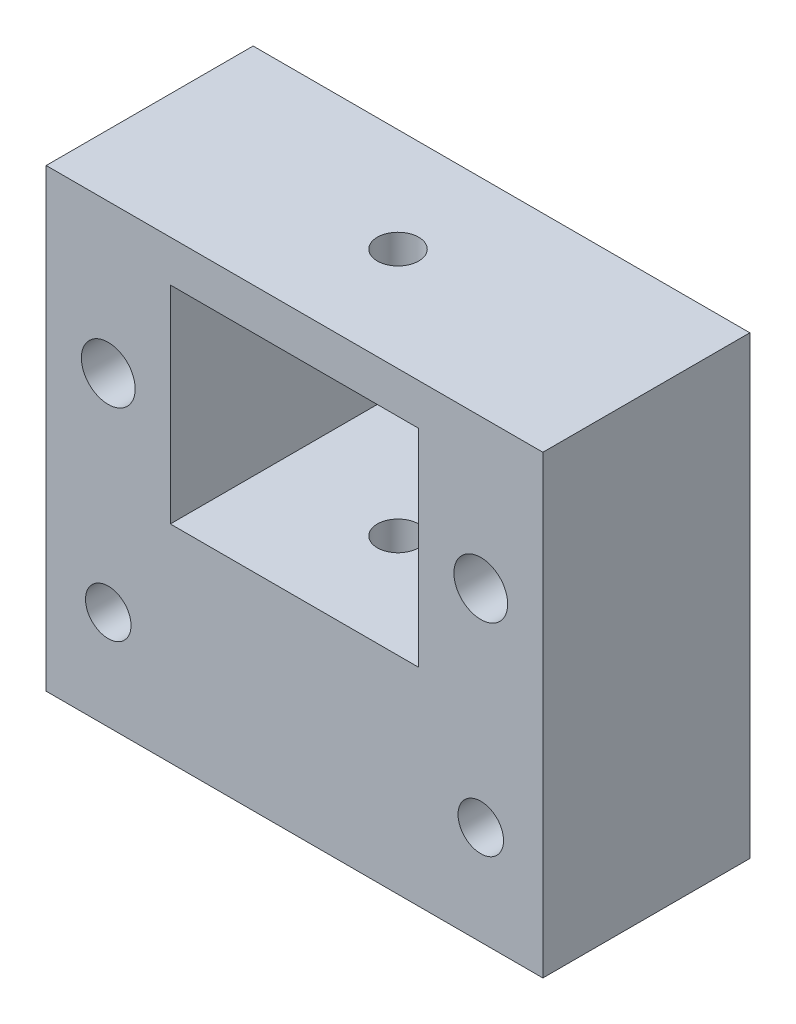
SolidWorks part; units mm, degrees
material "ABS PC"
ref_plane "Front Plane" through (0, 0, 0) normal (0, 0, 1) x (1, 0, 0)
ref_plane "Top Plane" through (0, 0, 0) normal (0, 1, 0) x (1, 0, 0)
ref_plane "Right Plane" through (0, 0, 0) normal (1, 0, 0) x (0, 0, -1)
sketch "Sketch2" plane through (0, 0, 0) normal (0, 1, 0) x (1, 0, 0)
  line L0 (0, 0) -> (0, 25)
  line L1 (0, 0) -> (60, 0)
  line L2 (0, 25) -> (60, 25)
  line L3 (60, 0) -> (60, 25)
  dimension "D1" = 25
  dimension "D2" = 60
extrude "Boss-Extrude1" add sketch "Sketch2" along normal blind 55
sketch "Sketch3" plane through (0, 0, 0) normal (0, 0, 1) x (1, 0, 0)
  line L0 (15, 50) -> (15, 25)
  line L1 (15, 50) -> (45, 50)
  line L2 (15, 25) -> (45, 25)
  line L3 (45, 50) -> (45, 25)
  line L5 (0, 55) -> (0, 0) construction
  line L6 (0, 55) -> (60, 55) construction
  dimension "D1" = 30
  dimension "D2" = 15
  dimension "D3" = 25
  dimension "D4" = 5
extrude "Cut-Extrude1" cut sketch "Sketch3" against normal up to next
sketch "Sketch4" plane through (0, 55, 0) normal (0, 1, 0) x (1, 0, 0)
  line L0 (60, 25) -> (0, 25) construction
  line L1 (60, 0) -> (60, 25) construction
  circle A0 centre (30, 12.5) radius 2.5
  dimension "D1" = 5
  dimension "D2" = 12.5
  dimension "D3" = 30
extrude "Cut-Extrude2" cut sketch "Sketch4" against normal through all
sketch "Sketch5" plane through (0, 0, 0) normal (0, 0, 1) x (1, 0, 0)
  line L0 (0, 55) -> (0, 0) construction
  line L1 (60, 55) -> (60, 0) construction
  line L2 (0, 0) -> (60, 0) construction
  circle A0 centre (7.5, 37) radius 3.25
  circle A1 centre (7.5, 12) radius 2.75
  circle A2 centre (52.5, 12) radius 2.75
  circle A3 centre (52.5, 37) radius 3.25
  dimension "D1" = 5.5
  dimension "D2" = 7.5
  dimension "D3" = 7.5
  dimension "D4" = 12
  dimension "D5" = 25
  dimension "D6" = 6.5
extrude "Cut-Extrude3" cut sketch "Sketch5" against normal through all
sketch "Sketch9" plane through (0, 0, -25) normal (0, 0, -1) x (-1, 0, 0)
  circle A0 centre (-52.5, 37) radius 4.45
  circle A1 centre (-7.5, 37) radius 4.45
  dimension "D1" = 8.9
extrude "Cut-Extrude7" cut sketch "Sketch9" against normal blind 11.5
